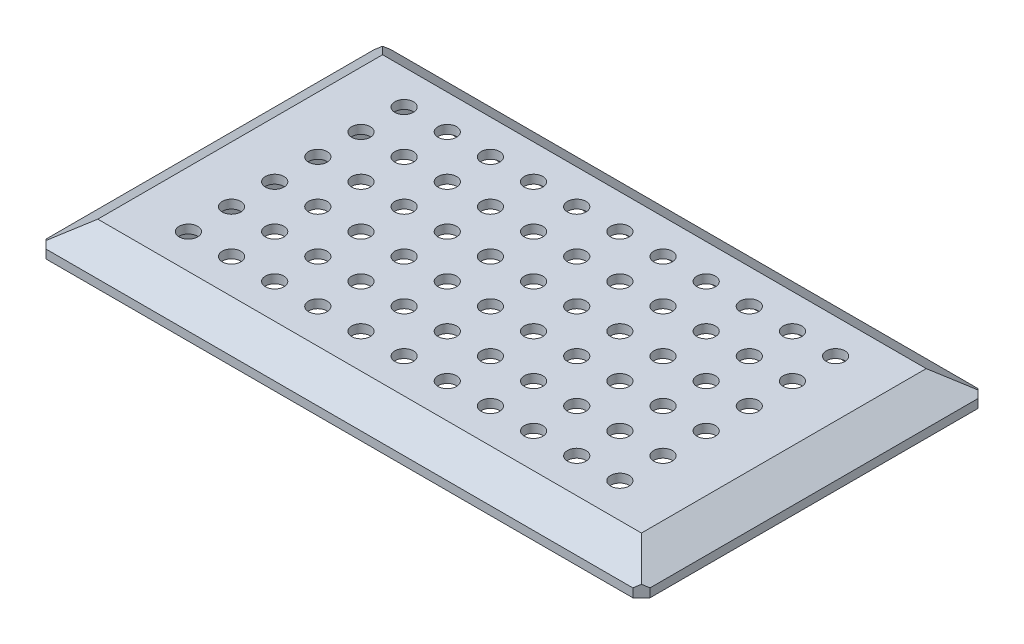
SolidWorks part; units mm, degrees
ref_plane "Front Plane" through (0, 0, 0) normal (0, 0, 1) x (1, 0, 0)
ref_plane "Top Plane" through (0, 0, 0) normal (0, 1, 0) x (1, 0, 0)
ref_plane "Right Plane" through (0, 0, 0) normal (1, 0, 0) x (0, 0, -1)
sketch "Sketch1" plane through (0, 0, 0) normal (0, 1, 0) x (1, 0, 0)
  line L1 (-70, -40) -> (70, -40)
  line L2 (-70, -40) -> (-70, 40)
  line L3 (-70, 40) -> (70, 40)
  line L4 (70, -40) -> (70, 40)
  line L5 (-70, -40) -> (70, 40) construction
  line L6 (-70, 40) -> (70, -40) construction
  point P0 (0, 0)
  dimension "D1" = 140
  dimension "D2" = 80
extrude "Boss-Extrude1" add sketch "Sketch1" along normal blind 2
sketch "Sketch2" plane through (0, 2, 0) normal (0, 1, 0) x (1, 0, 0)
  line L4 (70, -40) -> (70, 40)
  line L5 (70, 40) -> (-70, 40)
  line L6 (-70, 40) -> (-70, -40)
  line L7 (-70, -40) -> (70, -40)
  line L8 (70, -40) -> (70, 40)
  line L9 (70, 40) -> (-70, 40)
  line L10 (-70, 40) -> (-70, -40)
  line L11 (-70, -40) -> (70, -40)
  dimension "D1" = 0
ref_plane "Plane1" through (0, 7, 0) normal (0, 1, 0) x (1, 0, 0)
sketch "Sketch3" plane through (0, 7, 0) normal (0, 1, 0) x (1, 0, 0)
  line L0 (-70, 40) -> (-70, -40) construction
  line L1 (-63, -33) -> (63, -33)
  line L2 (-63, -33) -> (-63, 33)
  line L3 (-63, 33) -> (63, 33)
  line L4 (63, -33) -> (63, 33)
  line L5 (-63, -33) -> (63, 33) construction
  line L6 (-63, 33) -> (63, -33) construction
  line L7 (70, 40) -> (-70, 40) construction
  point P0 (0, 0)
  dimension "D1" = 7
  dimension "D2" = 7
loft "Loft1" add profiles "Sketch3", "Sketch2"
chamfer "Chamfer2" distance 2 angle 45 4 edges at (70, 1, 40) (70, 1, -40) (-70, 1, -40) (-70, 1, 40)
sketch "Sketch4" plane through (0, 0, 0) normal (0, -1, 0) x (1, 0, 0)
  line L0 (-70, -38) -> (-70, 38) construction
  line L1 (-62.9, 15) -> (-54.9, 15)
  line L2 (-62.9, 15) -> (-62.9, 25)
  line L3 (-62.9, 25) -> (-54.9, 25)
  line L4 (-54.9, 15) -> (-54.9, 25)
  line L5 (-62.9, 15) -> (-54.9, 25) construction
  line L6 (-62.9, 25) -> (-54.9, 15) construction
  line L7 (-70, 0) -> (70, 0) construction
  line L8 (70, 38) -> (70, -38) construction
  line L9 (0, 40) -> (0, -40) construction
  line L10 (-68, 40) -> (68, 40) construction
  line L11 (68, -40) -> (-68, -40) construction
  line L12 (-62.9, -25) -> (-54.9, -15) construction
  line L13 (-62.9, -15) -> (-54.9, -25) construction
  line L14 (-54.9, -15) -> (-54.9, -25)
  line L15 (-62.9, -25) -> (-54.9, -25)
  line L16 (-62.9, -15) -> (-62.9, -25)
  line L17 (-62.9, -15) -> (-54.9, -15)
  line L18 (62.9, -15) -> (54.9, -25) construction
  line L19 (62.9, -25) -> (54.9, -15) construction
  line L20 (62.9, 25) -> (54.9, 15) construction
  line L21 (62.9, 15) -> (54.9, 25) construction
  line L22 (62.9, -15) -> (54.9, -15)
  line L23 (62.9, -15) -> (62.9, -25)
  line L24 (62.9, -25) -> (54.9, -25)
  line L25 (54.9, -15) -> (54.9, -25)
  line L26 (54.9, 15) -> (54.9, 25)
  line L27 (62.9, 25) -> (54.9, 25)
  line L28 (62.9, 15) -> (62.9, 25)
  line L29 (62.9, 15) -> (54.9, 15)
  point P0 (-58.9, 20)
  point P21 (-58.9, -20)
  point P30 (58.9, -20)
  point P31 (58.9, 20)
  dimension "D1" = 10
  dimension "D2" = 7.1
  dimension "D3" = 8
  dimension "D4" = 40
extrude "Boss-Extrude2" add sketch "Sketch4" along normal blind 7
sketch "Sketch5" plane through (-62.9, 0, 0) normal (-1, 0, 0) x (0, 0, 1)
  line L0 (-15, 0) -> (-25, -7) construction
  line L1 (0, 0) -> (0, 50000) construction
  circle A0 centre (-20, -3.5) radius 2.05
  circle A1 centre (20, -3.5) radius 2.05
  dimension "D1" = 4.1
extrude "Cut-Extrude1" cut sketch "Sketch5" against normal through all
sketch "Sketch6" plane through (0, 0, 0) normal (0, -1, 0) x (1, 0, 0)
  line L0 (54.9, 25) -> (54.9, 15) construction
  line L1 (-53.9, -32) -> (53.9, -32)
  line L2 (-53.9, -32) -> (-53.9, 32)
  line L3 (-53.9, 32) -> (53.9, 32)
  line L4 (53.9, -32) -> (53.9, 32)
  line L5 (-53.9, -32) -> (53.9, 32) construction
  line L6 (-53.9, 32) -> (53.9, -32) construction
  line L8 (-63, 33) -> (63, 33) construction
  point P0 (0, 0)
  dimension "D1" = 1
  dimension "D2" = 1
extrude "Cut-Extrude2" cut sketch "Sketch6" against normal offset from surface (5 mm away) 2 up to face at (0, 7, 0)
sketch "Skizze1" plane through (0, 7, 0) normal (0, 1, 0) x (1, 0, 0)
  line L0 (-53.9, 0) -> (53.9, 0) construction
  line L1 (0, -32) -> (0, 32) construction
  line L2 (-50, -25) -> (50, 25) construction
  line L4 (63, -33) -> (63, 33)
  line L5 (63, 33) -> (-63, 33)
  line L6 (-63, 33) -> (-63, -33)
  line L7 (-63, -33) -> (63, -33)
  line L8 (63, -33) -> (63, 33) construction
  line L9 (63, 33) -> (-63, 33) construction
  line L10 (-63, 33) -> (-63, -33) construction
  line L11 (-63, -33) -> (63, -33) construction
  line L12 (53.9, -32) -> (53.9, 32)
  line L13 (-53.9, -32) -> (53.9, -32)
  line L14 (-53.9, 32) -> (-53.9, -32)
  line L15 (53.9, 32) -> (-53.9, 32)
  line L16 (53.9, -32) -> (53.9, 32) construction
  line L17 (-53.9, -32) -> (53.9, -32) construction
  line L18 (-53.9, 32) -> (-53.9, -32) construction
  line L19 (53.9, 32) -> (-53.9, 32) construction
  circle A0 centre (-50, -25) radius 2.15
  circle A1 centre (-40, -25) radius 2.15
  circle A2 centre (-30, -25) radius 2.15
  circle A3 centre (-20, -25) radius 2.15
  circle A4 centre (-10, -25) radius 2.15
  circle A5 centre (0, -25) radius 2.15
  circle A6 centre (10, -25) radius 2.15
  circle A7 centre (20, -25) radius 2.15
  circle A8 centre (30, -25) radius 2.15
  circle A9 centre (40, -25) radius 2.15
  circle A10 centre (50, -25) radius 2.15
  circle A11 centre (-40, -15) radius 2.15
  circle A12 centre (-30, -15) radius 2.15
  circle A13 centre (-20, -15) radius 2.15
  circle A14 centre (-10, -15) radius 2.15
  circle A15 centre (0, -15) radius 2.15
  circle A16 centre (10, -15) radius 2.15
  circle A17 centre (20, -15) radius 2.15
  circle A18 centre (30, -15) radius 2.15
  circle A19 centre (40, -15) radius 2.15
  circle A20 centre (50, -15) radius 2.15
  circle A21 centre (-40, -5) radius 2.15
  circle A22 centre (-30, -5) radius 2.15
  circle A23 centre (-20, -5) radius 2.15
  circle A24 centre (-10, -5) radius 2.15
  circle A25 centre (0, -5) radius 2.15
  circle A26 centre (10, -5) radius 2.15
  circle A27 centre (20, -5) radius 2.15
  circle A28 centre (30, -5) radius 2.15
  circle A29 centre (40, -5) radius 2.15
  circle A30 centre (50, -5) radius 2.15
  circle A31 centre (-40, 5) radius 2.15
  circle A32 centre (-30, 5) radius 2.15
  circle A33 centre (-20, 5) radius 2.15
  circle A34 centre (-10, 5) radius 2.15
  circle A35 centre (0, 5) radius 2.15
  circle A36 centre (10, 5) radius 2.15
  circle A37 centre (20, 5) radius 2.15
  circle A38 centre (30, 5) radius 2.15
  circle A39 centre (40, 5) radius 2.15
  circle A40 centre (50, 5) radius 2.15
  circle A41 centre (-40, 15) radius 2.15
  circle A42 centre (-30, 15) radius 2.15
  circle A43 centre (-20, 15) radius 2.15
  circle A44 centre (-10, 15) radius 2.15
  circle A45 centre (0, 15) radius 2.15
  circle A46 centre (10, 15) radius 2.15
  circle A47 centre (20, 15) radius 2.15
  circle A48 centre (30, 15) radius 2.15
  circle A49 centre (40, 15) radius 2.15
  circle A50 centre (50, 15) radius 2.15
  circle A51 centre (-40, 25) radius 2.15
  circle A52 centre (-30, 25) radius 2.15
  circle A53 centre (-20, 25) radius 2.15
  circle A54 centre (-10, 25) radius 2.15
  circle A55 centre (0, 25) radius 2.15
  circle A56 centre (10, 25) radius 2.15
  circle A57 centre (20, 25) radius 2.15
  circle A58 centre (30, 25) radius 2.15
  circle A59 centre (40, 25) radius 2.15
  circle A60 centre (50, 25) radius 2.15
  circle A61 centre (-50, -15) radius 2.15
  circle A62 centre (-50, -5) radius 2.15
  circle A63 centre (-50, 5) radius 2.15
  circle A64 centre (-50, 15) radius 2.15
  circle A65 centre (-50, 25) radius 2.15
  point P14 (0, 0)
  point P15 (0, 0)
  point P16 (0, 0)
  point P17 (0, 0)
  point P18 (0, 0)
  point P149 (0, 0)
  dimension "D3" = 11
  dimension "D5" = 4.3
  dimension "D1" = 0
  dimension "D2" = 0
  dimension "D4" = 6
extrude "Schnitt-Linear austragen2" cut sketch "Skizze1" against normal blind 10
